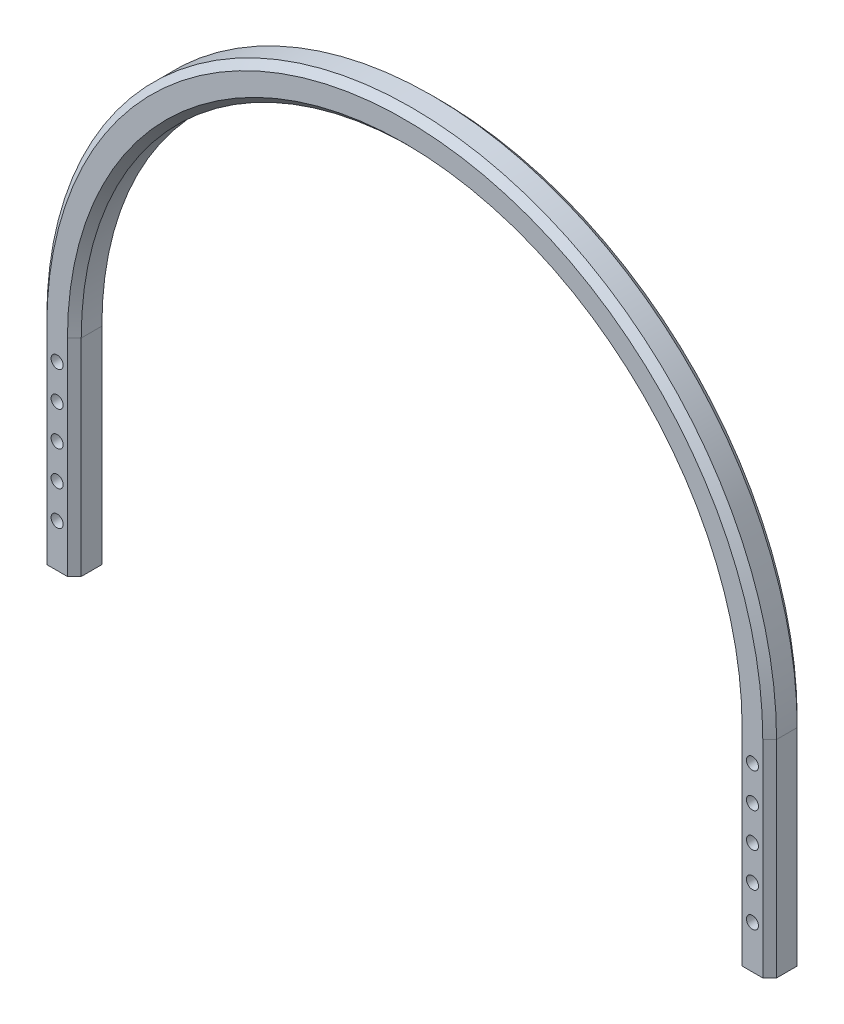
SolidWorks part; units mm, degrees
ref_plane "Front Plane" through (0, 0, 0) normal (0, 0, 1) x (1, 0, 0)
ref_plane "Top Plane" through (0, 0, 0) normal (0, 1, 0) x (1, 0, 0)
ref_plane "Right Plane" through (0, 0, 0) normal (1, 0, 0) x (0, 0, -1)
sketch "Sketch1" plane through (0, 0, 0) normal (0, 0, 1) x (1, 0, 0)
  line L0 (-106, 0) -> (106, 0) construction
  line L1 (-106, 0) -> (-106, 60)
  line L2 (-106, 60) -> (106, 60) construction
  line L3 (106, 60) -> (106, 0)
  line L4 (-96, 0) -> (-96, 60)
  line L5 (96, 60) -> (96, 0)
  line L6 (-106, 0) -> (-96, 0)
  line L7 (96, 0) -> (106, 0)
  arc A0 (-106, 60) -> (106, 60) centre (0, 60) cw
  arc A1 (-96, 60) -> (96, 60) centre (0, 60) cw
  dimension "D1" = 212
  dimension "D2" = 60
  dimension "D3" = 10
extrude "Boss-Extrude1" add sketch "Sketch1" along normal blind 10
chamfer "Chamfer1" distance 2 angle 45 12 edges at (-96, 30, 0) (0, 156, 0) (96, 30, 0) (-106, 30, 0) (0, 166, 0) (106, 30, 0) (-96, 30, 10) (0, 156, 10) (96, 30, 10) (-106, 30, 10) (0, 166, 10) (106, 30, 10)
sketch "Sketch2" plane through (0, 0, 10) normal (0, 0, 1) x (1, 0, 0)
  line L0 (-101, 0) -> (-101, 12.5) construction
  line L1 (-104, 0) -> (-98, 0) construction
  line L2 (0, -5.5) -> (0, 5.5) construction
  circle A0 centre (-101, 12.5) radius 1.75
  circle A1 centre (101, 12.5) radius 1.75
  dimension "D2" = 3.5
  dimension "D1" = 12.5
extrude "Cut-Extrude1" cut sketch "Sketch2" against normal through all
pattern_linear "LPattern1" count 5 spacing 10 along (0, 1, 0) of "Cut-Extrude1"
sketch "Sketch3" plane through (0, 0, 0) normal (0, -1, 0) x (1, 0, 0)
  line L0 (-101, 0) -> (-101, 5) construction
  line L1 (-104, 0) -> (-98, 0) construction
  line L2 (-101, 5) -> (-106, 5) construction
  line L3 (-106, 8) -> (-106, 2) construction
  line L4 (0, -5.5) -> (0, 5.5) construction
  circle A0 centre (-101, 5) radius 1.5
  circle A1 centre (101, 5) radius 1.5
  dimension "D1" = 3
extrude "Cut-Extrude2" cut sketch "Sketch3" against normal blind 10
